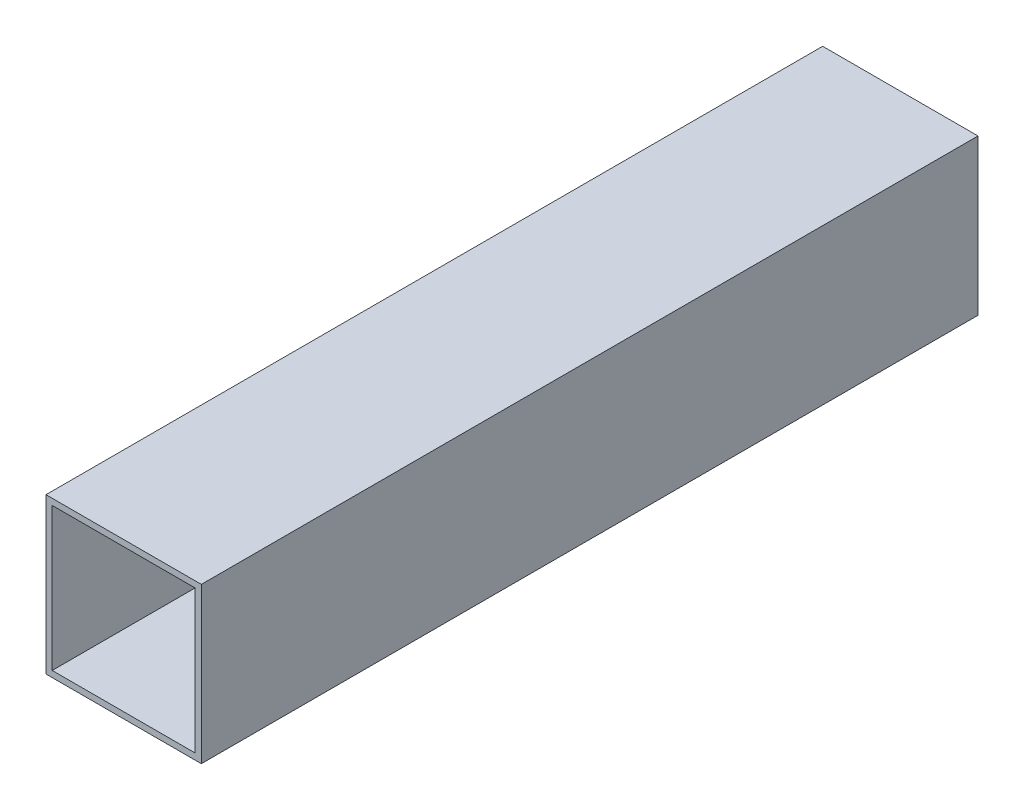
SolidWorks part; units mm, degrees
material "ABS"
ref_plane "Plano frontal" through (0, 0, 0) normal (0, 0, 1) x (1, 0, 0)
ref_plane "Plano superior" through (0, 0, 0) normal (0, 1, 0) x (1, 0, 0)
ref_plane "Plano direito" through (0, 0, 0) normal (1, 0, 0) x (0, 0, -1)
sketch "Esboço1" plane through (0, 0, 0) normal (0, 0, 1) x (1, 0, 0)
  line L1 (-20, -20) -> (20, -20)
  line L2 (-20, -20) -> (-20, 20)
  line L3 (-20, 20) -> (20, 20)
  line L4 (20, -20) -> (20, 20)
  line L5 (-20, -20) -> (20, 20) construction
  line L6 (-20, 20) -> (20, -20) construction
  line L7 (-18.4, -18.4) -> (18.4, -18.4)
  line L8 (-18.4, -18.4) -> (-18.4, 18.4)
  line L9 (-18.4, 18.4) -> (18.4, 18.4)
  line L10 (18.4, -18.4) -> (18.4, 18.4)
  line L11 (-18.4, -18.4) -> (18.4, 18.4) construction
  line L12 (-18.4, 18.4) -> (18.4, -18.4) construction
  point P0 (0, 0)
  point P6 (0, 0)
  dimension "D1" = 40
  dimension "D2" = 1.6
extrude "Ressalto-extrusão1" add sketch "Esboço1" along normal blind 200
